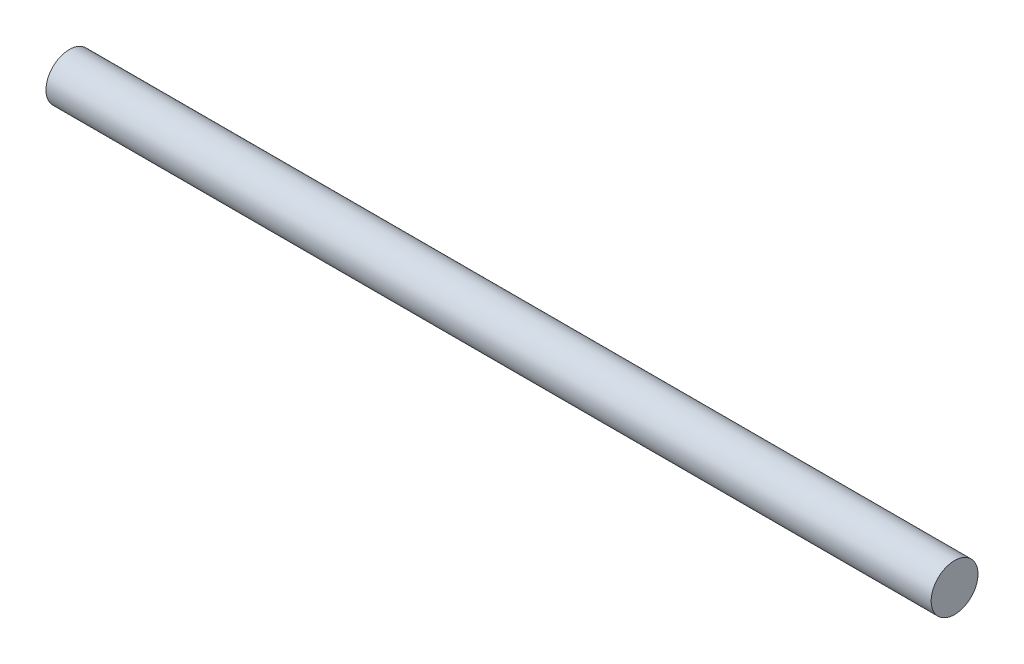
SolidWorks part; units mm, degrees
material "6061 Alloy"
ref_plane "Front Plane" through (0, 0, 0) normal (0, 0, 1) x (1, 0, 0)
ref_plane "Top Plane" through (0, 0, 0) normal (0, 1, 0) x (1, 0, 0)
ref_plane "Right Plane" through (0, 0, 0) normal (1, 0, 0) x (0, 0, -1)
other "Default"
sketch "Sketch1" plane through (0, 0, 0) normal (1, 0, 0) x (0, 0, -1)
  circle A0 centre (0, 0) radius 1.5875
  dimension "D1" = 3.175
extrude "Boss-Extrude1" add sketch "Sketch1" along normal mid plane 60
